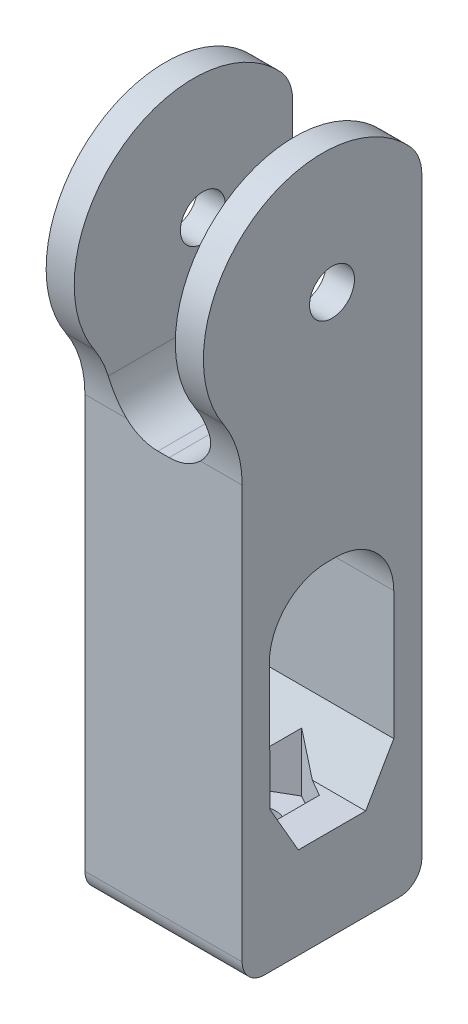
SolidWorks part; units mm, degrees
material "ABS generico"
ref_plane "Piano frontale" through (0, 0, 0) normal (0, 0, 1) x (1, 0, 0)
ref_plane "Piano superiore" through (0, 0, 0) normal (0, 1, 0) x (1, 0, 0)
ref_plane "Piano destro" through (0, 0, 0) normal (1, 0, 0) x (0, 0, -1)
sketch "Sketch9" plane through (0, 0, 0) normal (1, 0, 0) x (0, 0, -1)
  line L0 (8, 5.0539) -> (8, -49.642)
  line L1 (8, -49.642) -> (-8, -49.642)
  line L2 (-8, -49.642) -> (-8, -10.8758)
  line L3 (5.5, -41.5) -> (5.5, -25.7624)
  line L5 (0.3362, -20.5986) -> (-0.4104, -20.5986)
  line L6 (-5.5741, -25.7867) -> (-5.5, -41.5)
  line L7 (-5.5, -41.5) -> (5.5, -41.5)
  line L8 (0, -49.642) -> (0, 21.1385) construction
  circle A0 centre (0, 0) radius 2
  arc A1 (6.9253, 7.782) -> (-9.6743, -5.3367) centre (-0.8371, 0.5427) ccw
  arc A2 (-8, -10.8758) -> (-9.6743, -5.3367) centre (-18, -10.8758) ccw
  arc A3 (8, 5.0539) -> (6.9253, 7.782) centre (4, 5.0539) ccw
  arc A4 (5.5, -25.7624) -> (0.3362, -20.5986) centre (0.3362, -25.7624) ccw
  arc A5 (-5.5741, -25.7867) -> (-0.4104, -20.5986) centre (-0.4104, -25.7624) cw
  point P24 (8, 6.4221)
  dimension "D1" = 4
  dimension "D2" = 10
  dimension "D3" = 4
  dimension "D4" = 5.1638
  dimension "D5" = 16
extrude "Boss-Extrude3" add sketch "Sketch9" along normal blind 14
sketch "Sketch10" plane through (0, -49.642, 0) normal (0, -1, 0) x (1, 0, 0)
  line L0 (7, 8) -> (7, -8) construction
  line L1 (14, 8) -> (0, 8) construction
  line L2 (14, -8) -> (0, -8) construction
  line L3 (0, 0) -> (18.4029, 0) construction
  line L5 (0, 8) -> (0, -8) construction
  circle A0 centre (7, 0) radius 2
  point P11 (7, 0)
  dimension "D1" = 4
extrude "Cut-Extrude7" cut sketch "Sketch10" against normal blind 14
ref_plane "Plane1" through (0, 16, 0) normal (0, 1, 0) x (1, 0, 0)
sketch "Sketch11" plane through (0, 16, 0) normal (0, 1, 0) x (1, 0, 0)
  line L0 (7, 8) -> (7, -11.4514) construction
  line L1 (14, 8) -> (0, 8) construction
  line L2 (0, -11.4514) -> (14, -11.4514) construction
  line L4 (11.5, -16.0809) -> (2.5, -16.0809)
  line L5 (11.5, -16.0809) -> (11.5, 10.6052)
  line L6 (11.5, 10.6052) -> (2.5, 10.6052)
  line L7 (2.5, -16.0809) -> (2.5, 10.6052)
  line L8 (11.5, -16.0809) -> (2.5, 10.6052) construction
  line L9 (11.5, 10.6052) -> (2.5, -16.0809) construction
  point P6 (7, -2.7378)
  dimension "D1" = 9
extrude "Cut-Extrude8" cut sketch "Sketch11" against normal blind 28
fillet "Fillet1" radius 2 2 edges at (7, -49.642, -8) (7, -49.642, 8)
chamfer "Chamfer1" distance 2.5 angle 60 2 edges at (7, -41.5, 5.5) (7, -41.5, -5.5)
sketch "Sketch12" plane through (0, -41.5, 0) normal (0, 1, 0) x (1, 0, 0)
  line L1 (7, 4.3) -> (3.2761, 2.15)
  line L2 (3.2761, 2.15) -> (3.2761, -2.15)
  line L3 (3.2761, -2.15) -> (7, -4.3)
  line L4 (7, -4.3) -> (10.7239, -2.15)
  line L5 (10.7239, -2.15) -> (10.7239, 2.15)
  line L6 (10.7239, 2.15) -> (7, 4.3)
  circle A0 centre (7, 0) radius 4.3 construction
extrude "Extrude1" cut sketch "Sketch12" against normal blind 3 and the other way blind 3
fillet "Fillet2" radius 4 2 edges at (2.5, -12, 0) (11.5, -12, 0)
